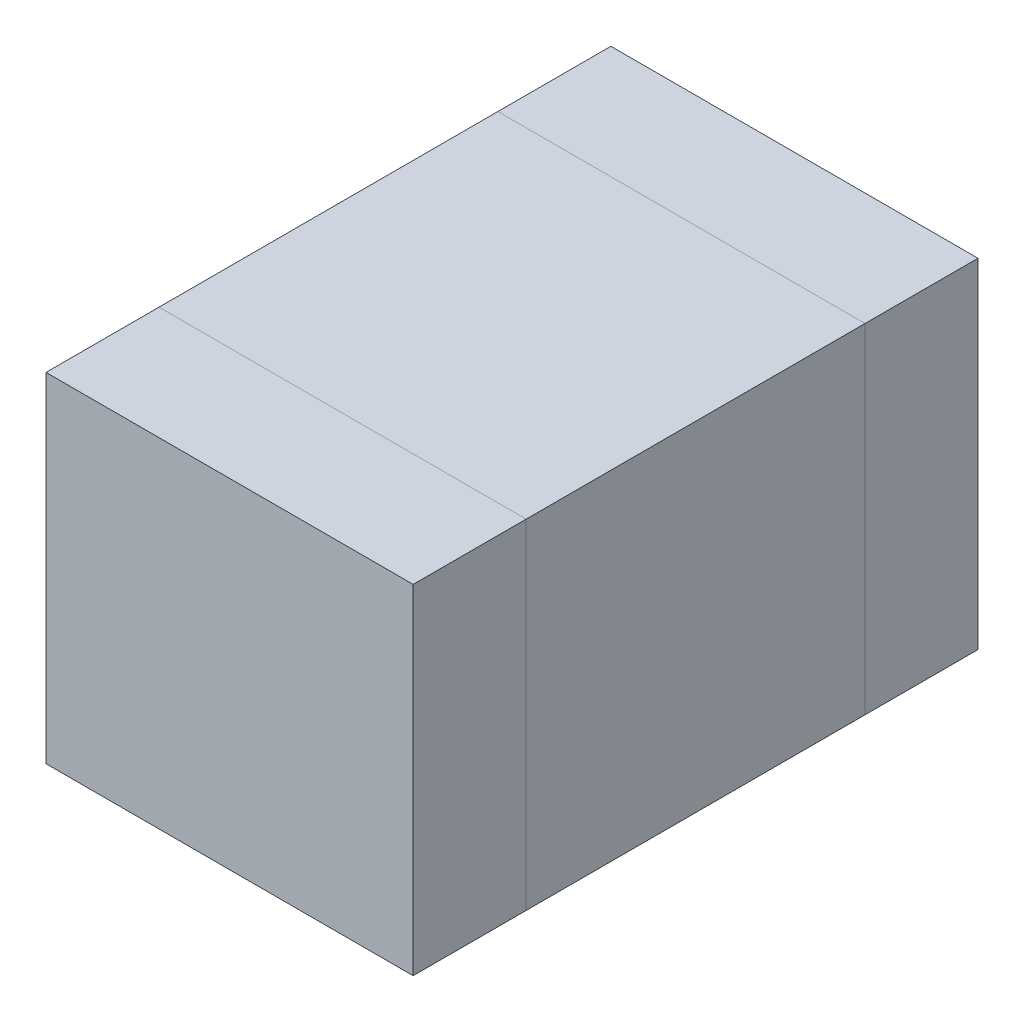
SolidWorks part; units mm, degrees
ref_plane "Front Plane" through (0, 0, 0) normal (0, 0, 1) x (1, 0, 0)
ref_plane "Top Plane" through (0, 0, 0) normal (0, 1, 0) x (1, 0, 0)
ref_plane "Right Plane" through (0, 0, 0) normal (1, 0, 0) x (0, 0, -1)
sketch "Sketch1" plane through (0, 0, 0) normal (0, 1, 0) x (1, 0, 0)
  line L1 (-0.65, 0.6) -> (0.65, 0.6)
  line L2 (-0.65, 0.6) -> (-0.65, -0.6)
  line L3 (-0.65, -0.6) -> (0.65, -0.6)
  line L4 (0.65, 0.6) -> (0.65, -0.6)
  line L5 (-0.65, 0.6) -> (0.65, -0.6) construction
  line L6 (-0.65, -0.6) -> (0.65, 0.6) construction
  point P0 (0, 0)
  dimension "D1" = 1.2
  dimension "D2" = 1.3
extrude "MB" add sketch "Sketch1" along normal blind 1.2
sketch "Sketch2" plane through (0, 0, 0.6) normal (0, 0, 1) x (1, 0, 0)
  line L4 (-0.65, 0) -> (0.65, 0)
  line L5 (0.65, 0) -> (0.65, 1.2)
  line L6 (0.65, 1.2) -> (-0.65, 1.2)
  line L7 (-0.65, 1.2) -> (-0.65, 0)
  line L8 (-0.65, 0) -> (0.65, 0)
  line L9 (0.65, 0) -> (0.65, 1.2)
  line L10 (0.65, 1.2) -> (-0.65, 1.2)
  line L11 (-0.65, 1.2) -> (-0.65, 0)
  dimension "D1" = 0
extrude "SB L" add sketch "Sketch2" along normal blind 0.4 separate body
sketch "Sketch3" plane through (0, 0, -0.6) normal (0, 0, -1) x (-1, 0, 0)
  line L4 (-0.65, 0) -> (0.65, 0)
  line L5 (0.65, 0) -> (0.65, 1.2)
  line L6 (0.65, 1.2) -> (-0.65, 1.2)
  line L7 (-0.65, 1.2) -> (-0.65, 0)
  line L8 (-0.65, 0) -> (0.65, 0)
  line L9 (0.65, 0) -> (0.65, 1.2)
  line L10 (0.65, 1.2) -> (-0.65, 1.2)
  line L11 (-0.65, 1.2) -> (-0.65, 0)
  dimension "D1" = 0
extrude "SB R" add sketch "Sketch3" along normal blind 0.4 separate body
